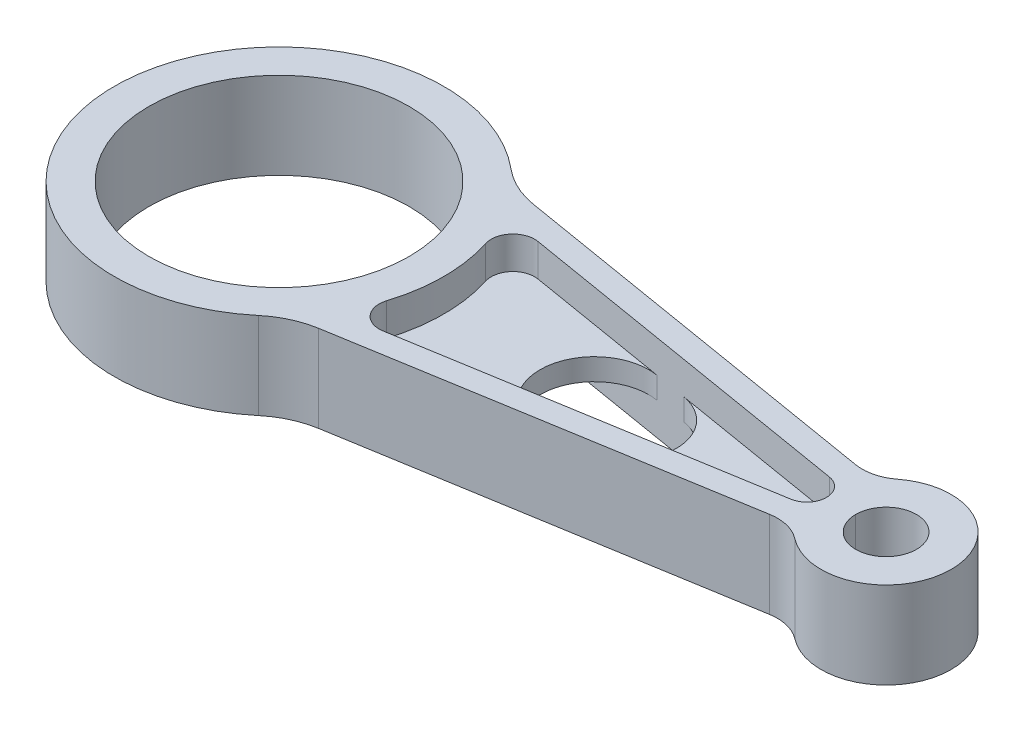
SolidWorks part; units mm, degrees
material "Plain Carbon Steel"
ref_plane "Front Plane" through (0, 0, 0) normal (0, 0, 1) x (1, 0, 0)
ref_plane "Top Plane" through (0, 0, 0) normal (0, 1, 0) x (1, 0, 0)
ref_plane "Right Plane" through (0, 0, 0) normal (1, 0, 0) x (0, 0, -1)
sketch "Sketch1" plane through (0, 0, 0) normal (0, 1, 0) x (1, 0, 0)
  line L0 (-48.1342, 0) -> (171.6981, 0) construction
  line L1 (27.9355, 25.7606) -> (128.0638, 9.0844)
  line L2 (128.0638, -9.0844) -> (27.9355, -25.7606)
  circle A0 centre (0, 0) radius 30
  circle A1 centre (140, 0) radius 7
  arc A2 (27.9355, 25.7606) -> (27.9355, -25.7606) centre (0, 0) ccw
  arc A3 (128.0638, -9.0844) -> (128.0638, 9.0844) centre (140, 0) ccw
  arc A4 (38, 0) -> (27.9355, 25.7606) centre (0, 0) ccw construction
  arc A5 (27.9355, -25.7606) -> (38, 0) centre (0, 0) ccw construction
  arc A6 (128.0638, 9.0844) -> (125, 0) centre (140, 0) ccw construction
  arc A7 (125, 0) -> (128.0638, -9.0844) centre (140, 0) ccw construction
  dimension "D2" = 14
  dimension "D3" = 60
  dimension "D4" = 76
  dimension "D5" = 30
  dimension "D1" = 140
extrude "Boss-Extrude1" add sketch "Sketch1" along normal mid plane 20
fillet "Fillet1" radius 10 2 edges at (128.0638, 0, 9.0844) (128.0638, 0, -9.0844)
fillet "Fillet2" radius 20 2 edges at (27.9355, 0, 25.7606) (27.9355, 0, -25.7606)
split line "Split Line4"
sketch "Sketch14" plane through (0, 10, 0) normal (0, 1, 0) x (1, 0, 0)
  line L0 (41.8286, 17.871) -> (122.4784, 4.4389)
  line L1 (122.4784, -4.4389) -> (41.8286, -17.871)
  line L2 (0, 0) -> (166.5822, 0) construction
  line L3 (123.0688, 9.9163) -> (33.9231, 24.7634) construction
  line L4 (33.9231, -24.7634) -> (123.0688, -9.9163) construction
  arc A0 (36.2389, 11.4344) -> (36.2389, -11.4344) centre (0, 0) cw
  arc A1 (122.4784, 4.4389) -> (122.4784, -4.4389) centre (121.7391, 0) cw
  arc A2 (36.2389, 11.4344) -> (41.8286, 17.871) centre (41.0071, 12.9389) cw
  arc A3 (36.2389, -11.4344) -> (41.8286, -17.871) centre (41.0071, -12.9389) ccw
  circle A5 centre (0, 0) radius 30 construction
  point P15 (0, 0)
  point P16 (0, 0)
  dimension "D1" = 5
  dimension "D2" = 4.5
  dimension "D3" = 5.5
  dimension "D4" = 8
sketch "Sketch12" plane through (0, 10, 0) normal (0, 1, 0) x (1, 0, 0)
  line L0 (41.8286, 17.871) -> (122.4784, 4.4389)
  line L1 (122.4784, -4.4389) -> (41.8286, -17.871)
  line L2 (0.5746, 0) -> (171.4896, 0) construction
  line L3 (33.9231, -24.7634) -> (123.0688, -9.9163) construction
  line L4 (123.0688, 9.9163) -> (33.9231, 24.7634) construction
  arc A1 (122.4784, 4.4389) -> (122.4784, -4.4389) centre (121.7391, 0) cw
  arc A2 (36.2389, 11.4344) -> (41.8286, 17.871) centre (41.0071, 12.9389) cw
  arc A3 (36.2389, -11.4344) -> (41.8286, -17.871) centre (41.0071, -12.9389) ccw
  circle A4 centre (0, 0) radius 30 construction
  arc A6 (36.2389, 11.4344) -> (36.2389, -11.4344) centre (0, 0) cw
  dimension "D1" = 5
  dimension "D2" = 4.5
  dimension "D4" = 8
  dimension "D3" = 5.5
extrude "Cut-Extrude4" cut sketch "Sketch14" against normal through all
sketch "Sketch11" plane through (0, 0, 0) normal (0, 1, 0) x (1, 0, 0)
  line L0 (41.8286, 17.871) -> (122.4784, 4.4389)
  line L1 (122.4784, -4.4389) -> (41.8286, -17.871)
  line L2 (123.0688, 9.9163) -> (33.9231, 24.7634) construction
  line L3 (33.9231, -24.7634) -> (123.0688, -9.9163) construction
  line L4 (0, 0) -> (140.0631, 0) construction
  arc A0 (36.2389, 11.4344) -> (36.2389, -11.4344) centre (0, 0) cw
  arc A1 (122.4784, 4.4389) -> (122.4784, -4.4389) centre (121.7391, 0) cw
  arc A2 (36.2389, 11.4344) -> (41.8286, 17.871) centre (41.0071, 12.9389) cw
  arc A3 (36.2389, -11.4344) -> (41.8286, -17.871) centre (41.0071, -12.9389) ccw
  circle A4 centre (0, 0) radius 30 construction
  dimension "D1" = 5
  dimension "D2" = 4.5
  dimension "D4" = 8
  dimension "D3" = 5.5
extrude "Boss-Extrude2" add sketch "Sketch11" along normal mid plane 5
sketch "Sketch2" plane through (0, 10, 0) normal (0, 1, 0) x (1, 0, 0)
  line L6 (74.8009, 12.3795) -> (82.1909, 11.1487)
  line L11 (123.0688, 9.9163) -> (33.9231, 24.7634) construction
  line L12 (82.1909, -11.1487) -> (74.8009, -12.3795)
  line L13 (-3.5152, 0) -> (167.3998, 0) construction
  line L15 (78.4959, 7.5004) -> (78.4959, -14.8094) construction
  line L16 (33.9231, -24.7634) -> (123.0688, -9.9163) construction
  arc A1 (74.8009, -12.3795) -> (74.8009, 12.3795) centre (72.7391, 0) cw
  arc A3 (82.1909, 11.1487) -> (82.1909, -11.1487) centre (80.3341, 0) cw
  point P1 (0, 0)
  point P2 (0, 0)
  point P6 (0, 0)
  point P7 (59.1412, 0)
  point P14 (0, 0)
  point P15 (0, 0)
  point P20 (0, 0)
  point P21 (78.4959, 11.7641)
  point P22 (78.4959, 17.3398)
  point P23 (0, 0)
  point P24 (0, 0)
  point P26 (87.4879, 0)
  point P27 (92.7725, 0)
  point P28 (71.5542, 0)
  point P29 (0, 0)
  point P30 (0, 0)
  point P31 (72.5909, 0)
  dimension "D1" = 12.55
  dimension "D3" = 5.5
extrude "Cut-Extrude3" cut sketch "Sketch2" against normal through all
